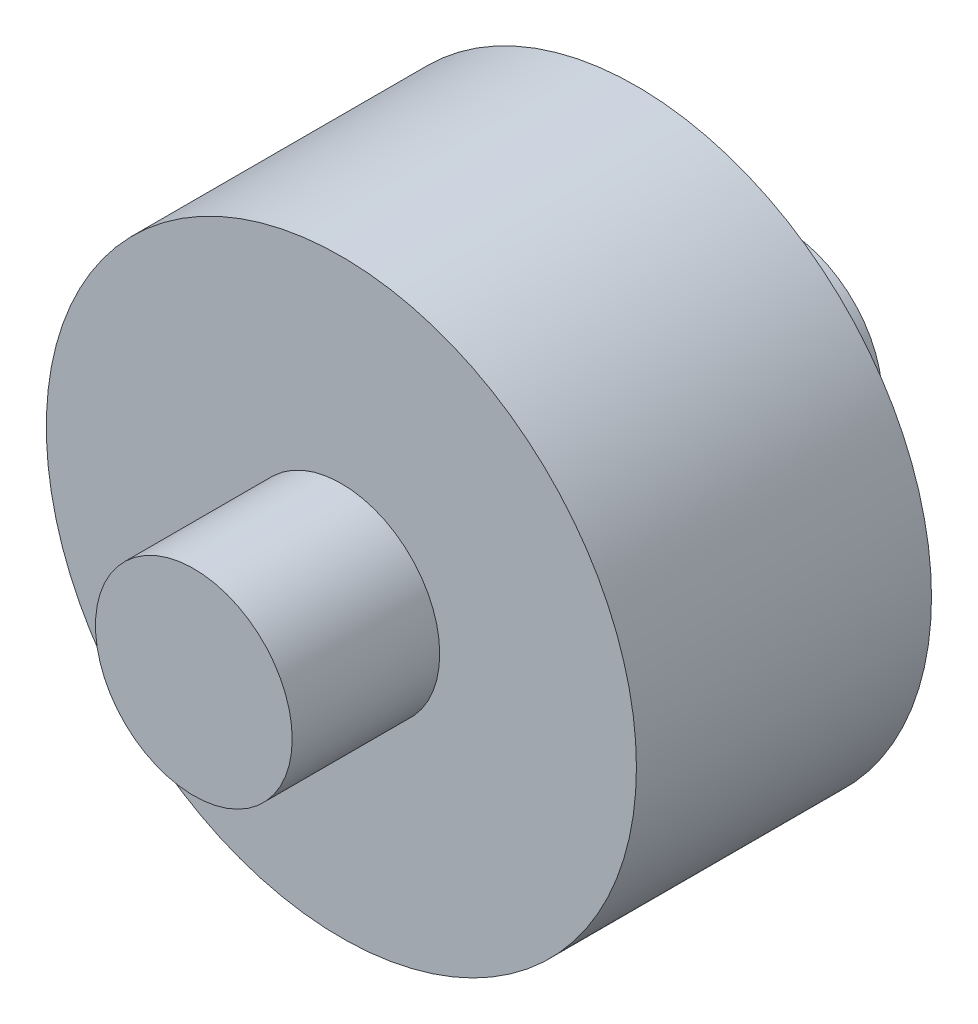
SolidWorks part; units mm, degrees
ref_plane "Front Plane" through (0, 0, 0) normal (0, 0, 1) x (1, 0, 0)
ref_plane "Top Plane" through (0, 0, 0) normal (0, 1, 0) x (1, 0, 0)
ref_plane "Right Plane" through (0, 0, 0) normal (1, 0, 0) x (0, 0, -1)
sketch "Sketch1" plane through (0, 0, 0) normal (0, 0, 1) x (1, 0, 0)
  circle A0 centre (0, 0) radius 9.525
  dimension "D1" = 19.05
extrude "Boss-Extrude1" add sketch "Sketch1" along normal mid plane 9.525
sketch "Sketch2" plane through (0, 0, 0) normal (0, 0, 1) x (1, 0, 0)
  circle A0 centre (0, 0) radius 3.175
  dimension "D1" = 6.35
extrude "Boss-Extrude2" add sketch "Sketch2" along normal mid plane 19.05
sketch "Sketch3" plane through (0, 0, 0) normal (1, 0, 0) x (0, 0, -1)
  circle A0 centre (0, 0) radius 3.175
  dimension "D1" = 6.35
extrude "Cut-Extrude3" cut sketch "Sketch3" against normal through all
